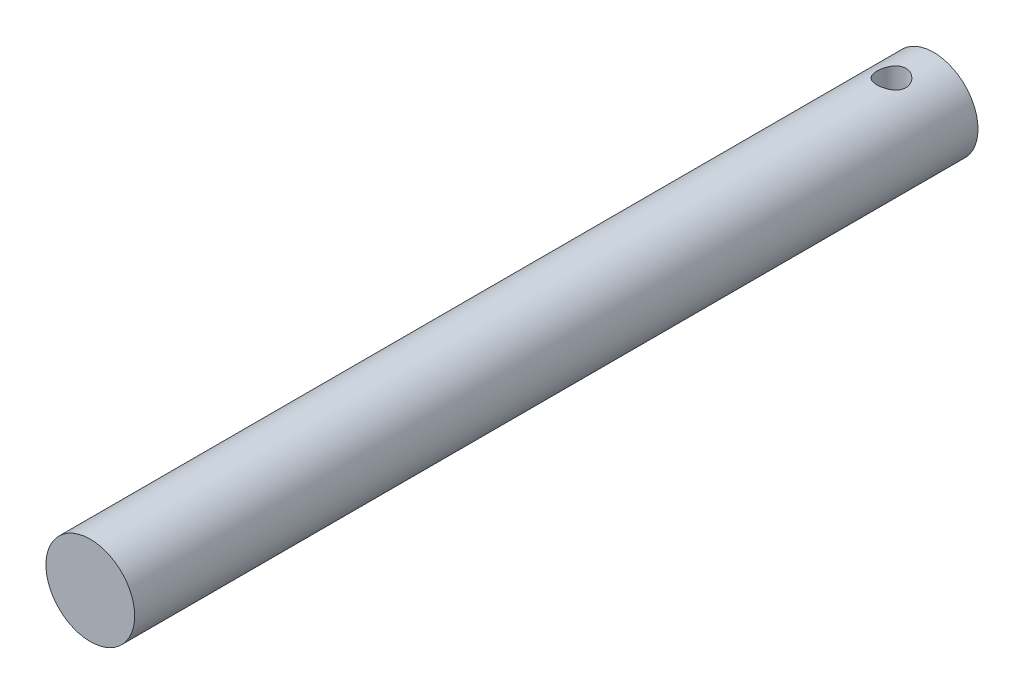
SolidWorks part; units mm, degrees
ref_plane "前视基准面" through (0, 0, 0) normal (0, 0, 1) x (1, 0, 0)
ref_plane "上视基准面" through (0, 0, 0) normal (0, 1, 0) x (1, 0, 0)
ref_plane "右视基准面" through (0, 0, 0) normal (1, 0, 0) x (0, 0, -1)
sketch "草图1" plane through (0, 0, 0) normal (0, 0, 1) x (1, 0, 0)
  circle A0 centre (0, 0) radius 10
  dimension "D1" = 20
extrude "凸台-拉伸1" add sketch "草图1" along normal blind 190
sketch "草图2" plane through (0, 0, 0) normal (0, 1, 0) x (1, 0, 0)
  line L0 (0, 19.453) -> (0, -26.2878) construction
  line L1 (10, 0) -> (-10, 0) construction
  circle A0 centre (0, -9.5) radius 3.25
  dimension "D1" = 6.5
  dimension "D2" = 9.5
extrude "切除-拉伸1" cut sketch "草图2" against normal mid plane 420
